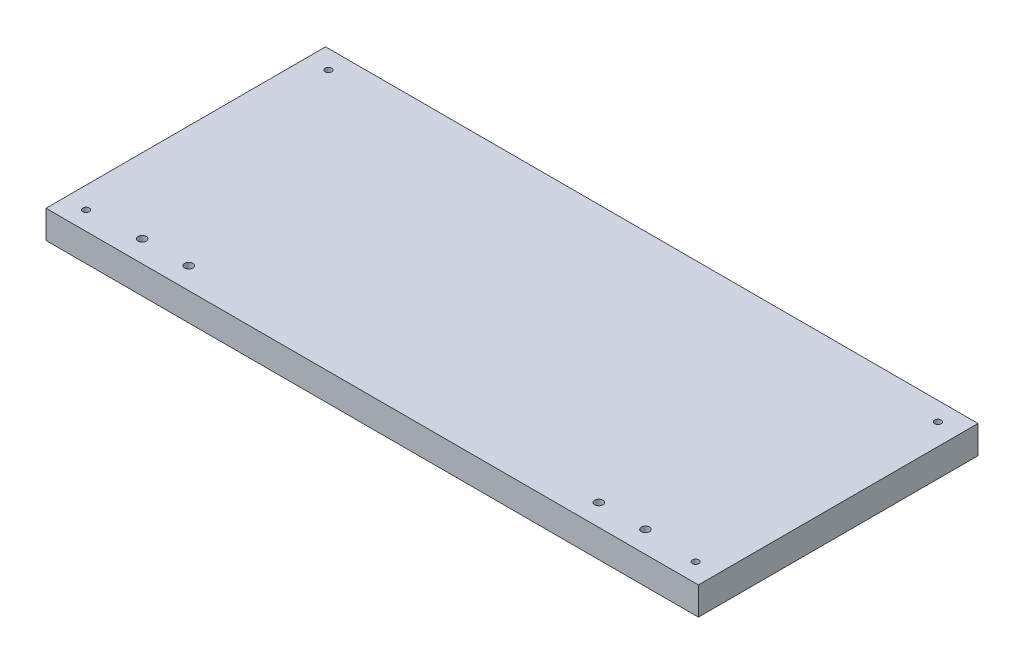
SolidWorks part; units mm, degrees
ref_plane "Front Plane" through (0, 0, 0) normal (0, 0, 1) x (1, 0, 0)
ref_plane "Top Plane" through (0, 0, 0) normal (0, 1, 0) x (1, 0, 0)
ref_plane "Right Plane" through (0, 0, 0) normal (1, 0, 0) x (0, 0, -1)
sketch "Sketch1" plane through (0, 0, 0) normal (0, 1, 0) x (1, 0, 0)
  line L0 (-163.5, 89.934) -> (-163.5, -97.6832) construction
  line L1 (-175, 75) -> (175, 75)
  line L2 (-175, 75) -> (-175, -75)
  line L3 (-175, -75) -> (175, -75)
  line L4 (175, 75) -> (175, -75)
  line L5 (-175, 75) -> (175, -75) construction
  line L6 (-175, -75) -> (175, 75) construction
  line L7 (163.5, 81.0723) -> (163.5, -97.6832) construction
  circle A0 centre (163.5, 65) radius 1.75
  circle A1 centre (163.5, -65) radius 1.75
  circle A2 centre (-163.5, -65) radius 1.75
  circle A3 centre (-163.5, 65) radius 1.75
  point P0 (0, 0)
  dimension "D5" = 3.5
  dimension "D1" = 350
  dimension "D2" = 150
  dimension "D3" = 11.5
  dimension "D4" = 11.5
  dimension "D6" = 10
  dimension "D7" = 10
  dimension "D8" = 10
  dimension "D9" = 10
extrude "Boss-Extrude1" add sketch "Sketch1" along normal blind 15
sketch "Sketch2" plane through (0, 15, 0) normal (0, 1, 0) x (1, 0, 0)
  line L0 (-175, 75) -> (-175, -75) construction
  line L1 (-175, -75) -> (175, -75) construction
  line L2 (175, -75) -> (175, 75) construction
  circle A0 centre (-135, -63.4) radius 2.2
  circle A1 centre (-110, -63.4) radius 2.2
  circle A2 centre (135, -63.4) radius 2.2
  circle A3 centre (110, -63.4) radius 2.2
  dimension "D1" = 4.4
  dimension "D5" = 4.4
  dimension "D2" = 40
  dimension "D3" = 11.6
  dimension "D6" = 11.6
  dimension "D7" = 40
  dimension "D4" = 2
  dimension "D8" = 2
extrude "Cut-Extrude1" cut sketch "Sketch2" against normal through all
